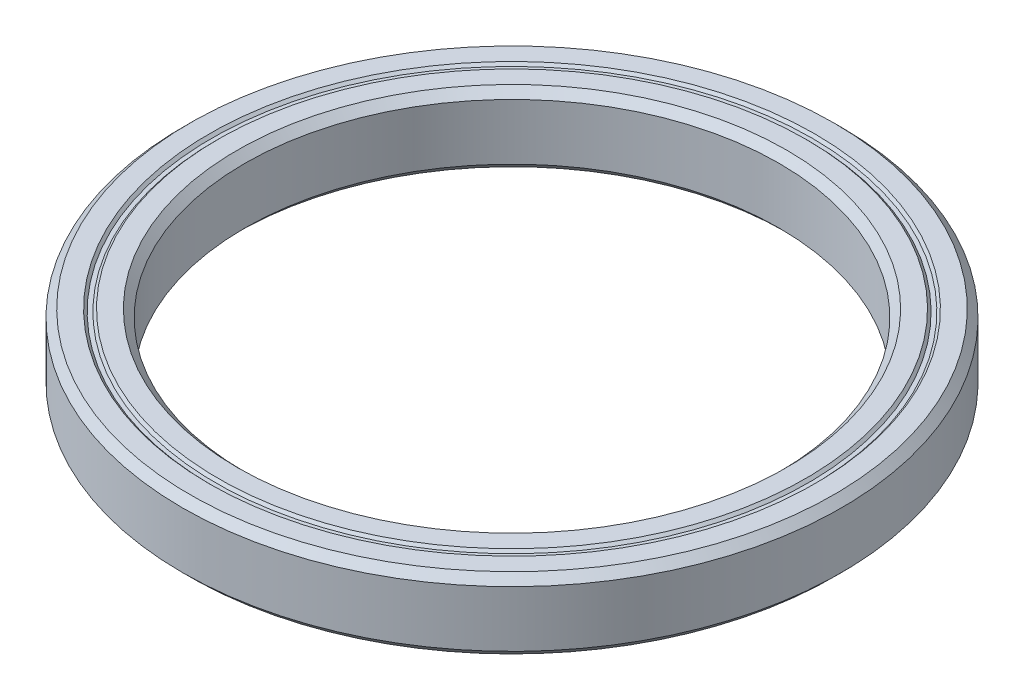
SolidWorks part; units mm, degrees
material "Stainless Steel (ferritic)"
ref_plane "Front Plane" through (0, 0, 0) normal (0, 0, 1) x (1, 0, 0)
ref_plane "Top Plane" through (0, 0, 0) normal (0, 1, 0) x (1, 0, 0)
ref_plane "Right Plane" through (0, 0, 0) normal (1, 0, 0) x (0, 0, -1)
sketch "Sketch1" plane through (0, 0, 0) normal (0, 0, 1) x (1, 0, 0)
  line L0 (0, -1.3494) -> (0, 70.5256) construction
  line L1 (15, 1.5731) -> (15, -1.5731)
  line L2 (15, -1.5731) -> (15.4269, -2)
  line L3 (15.4269, -2) -> (16.4941, -2)
  line L4 (16.4941, -2) -> (16.6364, -1.8577)
  line L5 (16.6364, -1.8577) -> (16.8636, -1.8577)
  line L6 (16.8636, -1.8577) -> (17.0059, -2)
  line L7 (17.0059, -2) -> (18.0731, -2)
  line L8 (18.0731, -2) -> (18.5, -1.5731)
  line L9 (18.5, -1.5731) -> (18.5, 1.5731)
  line L10 (18.5, 1.5731) -> (18.0731, 2)
  line L11 (18.0731, 2) -> (17.0059, 2)
  line L12 (17.0059, 2) -> (16.8636, 1.8577)
  line L13 (16.8636, 1.8577) -> (16.6364, 1.8577)
  line L14 (16.6364, 1.8577) -> (16.4941, 2)
  line L15 (16.4941, 2) -> (15.4269, 2)
  line L16 (15.4269, 2) -> (15, 1.5731)
  line L17 (0, 0) -> (15, 0) construction
  dimension "D1" = 15
  dimension "D2" = 4
  dimension "D3" = 0.4269
  dimension "D4" = 0.1423
  dimension "D5" = 18.5
  dimension "D6" = 1.0673
revolve "Revolve1" add sketch "Sketch1" angle 360 about L0
